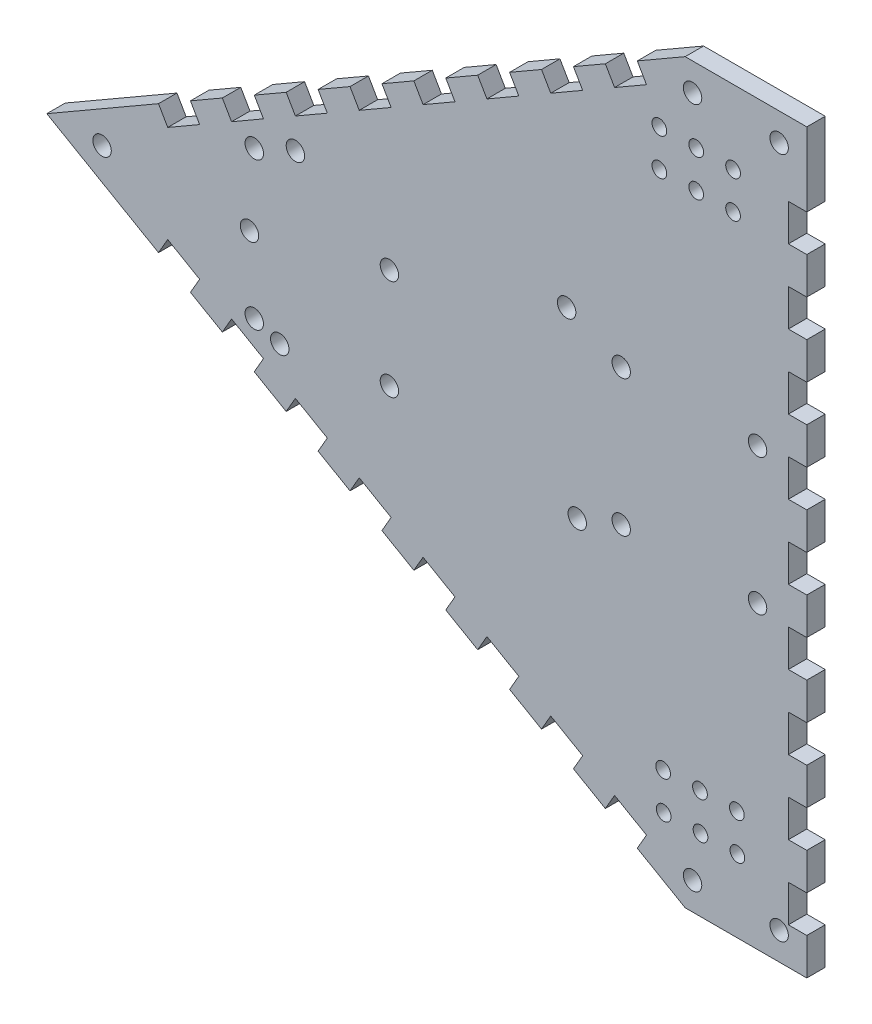
SolidWorks part; units mm, degrees
ref_plane "Front Plane" through (0, 0, 0) normal (0, 0, 1) x (1, 0, 0)
ref_plane "Top Plane" through (0, 0, 0) normal (0, 1, 0) x (1, 0, 0)
ref_plane "Right Plane" through (0, 0, 0) normal (1, 0, 0) x (0, 0, -1)
sketch "Sketch1" plane through (0, 0, 0) normal (0, 0, 1) x (1, 0, 0)
  line L0 (2.5, 0) -> (-30.5, 0)
  line L1 (2.5, 0) -> (-30.5, 0)
  line L2 (2.5, 0) -> (2.5, -200)
  line L3 (2.5, -200) -> (-30.5, -200)
  line L4 (-17.5, -20) -> (-27.5, -20) construction
  line L5 (-203.7051, -100) -> (-30.5, 0)
  line L7 (-30.5, -200) -> (-203.7051, -100)
  line L8 (-201.1315, -101.4859) -> (2.5, -100) construction
  line L9 (-2.5, 0) -> (2.5, 0)
  line L10 (2.5, 0) -> (-2.5, 0)
  line L15 (2.5, 0) -> (-2.5, 0)
  circle A0 centre (-17.5, -20) radius 2
  circle A1 centre (-27.5, -20) radius 2
  circle A2 centre (-37.5, -20) radius 2
  circle A3 centre (-27.5, -30) radius 2
  circle A4 centre (-37.5, -30) radius 2
  circle A5 centre (-17.5, -30) radius 2
  circle A6 centre (-36.3283, -180.5752) radius 2
  circle A7 centre (-26.3294, -180.4293) radius 2
  circle A8 centre (-26.4753, -170.4303) radius 2
  circle A9 centre (-16.4764, -170.2844) radius 2
  circle A10 centre (-16.3304, -180.2833) radius 2
  circle A11 centre (-36.4742, -170.5763) radius 2
  dimension "D8" = 4
  dimension "D2" = 60
  dimension "D3" = 200
  dimension "D4" = 188.4551
  dimension "D5" = 200
  dimension "D11" = 10
  dimension "D9" = 3
  dimension "D10" = 2
extrude "Boss-Extrude1" add sketch "Sketch1" along normal blind 5
sketch "Sketch2" plane through (0, 0, 5) normal (0, 0, 1) x (1, 0, 0)
  line L3 (-2.5, -100) -> (-136.8791, -100) construction
  circle A0 centre (-188.7051, -100) radius 2.5
  circle A1 centre (-5, -192.5) radius 2.5
  circle A2 centre (-10.85, -118.6057) radius 2.5
  circle A3 centre (-47.85, -118.6057) radius 2.5
  circle A4 centre (-5, -7.5) radius 2.5
  circle A5 centre (-47.85, -81.6057) radius 2.5
  circle A6 centre (-28.4904, -192.5) radius 2.5
  circle A7 centre (-10.85, -81.6057) radius 2.5
  circle A8 centre (-28.4904, -7.5) radius 2.5
  point P13 (2.5, -100.4557)
  dimension "D6" = 5
  dimension "D9" = 2
  dimension "D5" = 5
  dimension "D10" = 5
  dimension "D11" = 2
  dimension "D4" = 5
extrude "Cut-Extrude1" cut sketch "Sketch2" against normal through all both and the other way through all
sketch "Sketch3" plane through (0, 0, 5) normal (0, 0, 1) x (1, 0, 0)
  line L0 (-121.4327, -52.5) -> (-112.7724, -47.5)
  line L1 (-112.7724, -47.5) -> (-110.2724, -51.8301)
  line L2 (-110.2724, -51.8301) -> (-118.9327, -56.8301)
  line L3 (-118.9327, -56.8301) -> (-121.4327, -52.5)
  line L4 (-101.6122, -46.8301) -> (-104.1122, -42.5)
  line L5 (-92.9519, -41.8301) -> (-101.6122, -46.8301)
  line L6 (-95.4519, -37.5) -> (-92.9519, -41.8301)
  line L7 (-104.1122, -42.5) -> (-95.4519, -37.5)
  line L8 (-84.2917, -36.8301) -> (-86.7917, -32.5)
  line L9 (-75.6314, -31.8301) -> (-84.2917, -36.8301)
  line L10 (-78.1314, -27.5) -> (-75.6314, -31.8301)
  line L11 (-86.7917, -32.5) -> (-78.1314, -27.5)
  line L12 (-66.9711, -26.8301) -> (-69.4711, -22.5)
  line L13 (-58.3109, -21.8301) -> (-66.9711, -26.8301)
  line L14 (-60.8109, -17.5) -> (-58.3109, -21.8301)
  line L15 (-69.4711, -22.5) -> (-60.8109, -17.5)
  line L16 (-49.6506, -16.8301) -> (-52.1506, -12.5)
  line L17 (-40.9904, -11.8301) -> (-49.6506, -16.8301)
  line L18 (-43.4904, -7.5) -> (-40.9904, -11.8301)
  line L19 (-52.1506, -12.5) -> (-43.4904, -7.5)
  line L20 (-136.2532, -66.8301) -> (-138.7532, -62.5)
  line L21 (-127.5929, -61.8301) -> (-136.2532, -66.8301)
  line L22 (-130.0929, -57.5) -> (-127.5929, -61.8301)
  line L23 (-138.7532, -62.5) -> (-130.0929, -57.5)
  line L24 (-153.5737, -76.8301) -> (-156.0737, -72.5)
  line L25 (-144.9134, -71.8301) -> (-153.5737, -76.8301)
  line L26 (-147.4134, -67.5) -> (-144.9134, -71.8301)
  line L27 (-156.0737, -72.5) -> (-147.4134, -67.5)
  line L28 (-170.8942, -86.8301) -> (-173.3942, -82.5)
  line L29 (-162.2339, -81.8301) -> (-170.8942, -86.8301)
  line L30 (-164.7339, -77.5) -> (-162.2339, -81.8301)
  line L31 (-173.3942, -82.5) -> (-164.7339, -77.5)
  line L36 (-203.7051, -100) -> (-2.5, -100) construction
  line L39 (-112.7724, -152.5) -> (-110.2724, -148.1699)
  line L40 (-110.2724, -148.1699) -> (-118.9327, -143.1699)
  line L41 (-173.3942, -117.5) -> (-164.7339, -122.5)
  line L42 (-164.7339, -122.5) -> (-162.2339, -118.1699)
  line L43 (-156.0737, -127.5) -> (-147.4134, -132.5)
  line L44 (-147.4134, -132.5) -> (-144.9134, -128.1699)
  line L45 (-144.9134, -128.1699) -> (-153.5737, -123.1699)
  line L46 (-153.5737, -123.1699) -> (-156.0737, -127.5)
  line L47 (-138.7532, -137.5) -> (-130.0929, -142.5)
  line L48 (-130.0929, -142.5) -> (-127.5929, -138.1699)
  line L49 (-127.5929, -138.1699) -> (-136.2532, -133.1699)
  line L50 (-136.2532, -133.1699) -> (-138.7532, -137.5)
  line L55 (-162.2339, -118.1699) -> (-170.8942, -113.1699)
  line L56 (-170.8942, -113.1699) -> (-173.3942, -117.5)
  line L57 (-52.1506, -187.5) -> (-43.4904, -192.5)
  line L58 (-43.4904, -192.5) -> (-40.9904, -188.1699)
  line L59 (-40.9904, -188.1699) -> (-49.6506, -183.1699)
  line L60 (-49.6506, -183.1699) -> (-52.1506, -187.5)
  line L61 (-69.4711, -177.5) -> (-60.8109, -182.5)
  line L62 (-60.8109, -182.5) -> (-58.3109, -178.1699)
  line L63 (-58.3109, -178.1699) -> (-66.9711, -173.1699)
  line L64 (-66.9711, -173.1699) -> (-69.4711, -177.5)
  line L65 (-86.7917, -167.5) -> (-78.1314, -172.5)
  line L66 (-78.1314, -172.5) -> (-75.6314, -168.1699)
  line L67 (-75.6314, -168.1699) -> (-84.2917, -163.1699)
  line L68 (-84.2917, -163.1699) -> (-86.7917, -167.5)
  line L69 (-104.1122, -157.5) -> (-95.4519, -162.5)
  line L70 (-95.4519, -162.5) -> (-92.9519, -158.1699)
  line L71 (-92.9519, -158.1699) -> (-101.6122, -153.1699)
  line L72 (-101.6122, -153.1699) -> (-104.1122, -157.5)
  line L73 (-118.9327, -143.1699) -> (-121.4327, -147.5)
  line L74 (-121.4327, -147.5) -> (-112.7724, -152.5)
  line L75 (-2.5, -80) -> (-2.5, -90)
  line L76 (-2.5, -100) -> (2.5, -100)
  line L77 (-2.5, -100) -> (-2.5, -110)
  line L78 (-2.5, -110) -> (2.5, -110)
  line L79 (2.5, -100) -> (2.5, -110)
  line L80 (-2.5, -80) -> (2.5, -80)
  line L81 (2.5, -80) -> (2.5, -90)
  line L82 (-2.5, -90) -> (2.5, -90)
  line L83 (-2.5, -60) -> (-2.5, -70)
  line L84 (-2.5, -60) -> (2.5, -60)
  line L85 (2.5, -60) -> (2.5, -70)
  line L86 (-2.5, -70) -> (2.5, -70)
  line L87 (-2.5, -40) -> (-2.5, -50)
  line L88 (-2.5, -40) -> (2.5, -40)
  line L89 (2.5, -40) -> (2.5, -50)
  line L90 (-2.5, -50) -> (2.5, -50)
  line L91 (-2.5, -20) -> (-2.5, -30)
  line L92 (-2.5, -20) -> (2.5, -20)
  line L93 (2.5, -20) -> (2.5, -30)
  line L94 (-2.5, -30) -> (2.5, -30)
  line L99 (-2.5, -120) -> (-2.5, -130)
  line L100 (-2.5, -120) -> (2.5, -120)
  line L101 (2.5, -120) -> (2.5, -130)
  line L102 (-2.5, -130) -> (2.5, -130)
  line L103 (-2.5, -140) -> (-2.5, -150)
  line L104 (-2.5, -140) -> (2.5, -140)
  line L105 (2.5, -140) -> (2.5, -150)
  line L106 (-2.5, -150) -> (2.5, -150)
  line L107 (-2.5, -160) -> (-2.5, -170)
  line L108 (-2.5, -160) -> (2.5, -160)
  line L109 (2.5, -160) -> (2.5, -170)
  line L110 (-2.5, -170) -> (2.5, -170)
  line L111 (-2.5, -180) -> (-2.5, -190)
  line L112 (-2.5, -180) -> (2.5, -180)
  line L113 (2.5, -180) -> (2.5, -190)
  line L114 (-2.5, -190) -> (2.5, -190)
  line L129 (-179.5544, -91.8301) -> (-188.2147, -96.8301) [skipped]
  line L130 (-182.0544, -87.5) -> (-179.5544, -91.8301) [skipped]
  line L131 (-188.2147, -96.8301) -> (-190.7147, -92.5) [skipped]
  line L132 (-190.7147, -92.5) -> (-182.0544, -87.5) [skipped]
  line L133 (-2.5, 0) -> (2.5, 0) [skipped]
  line L134 (2.5, 0) -> (2.5, -10) [skipped]
  line L135 (-2.5, 0) -> (-2.5, -10) [skipped]
  line L136 (-2.5, -10) -> (2.5, -10) [skipped]
  circle A0 centre (-136.2532, -75) radius 2.5
  circle A1 centre (-62.6532, -75) radius 2.5
  circle A2 centre (-140.4956, -122.5) radius 2.5
  circle A3 centre (-59.7756, -123.1699) radius 2.5
  circle A4 centre (-110.7456, -117.5) radius 2.5
  circle A5 centre (-110.7456, -90.25) radius 2.5
  circle A6 centre (-148.7051, -100) radius 2.5
  circle A7 centre (-147.4134, -80) radius 2.5
  circle A8 centre (-147.4134, -120) radius 2.5
  point P15 (-151.7436, -130)
  point P16 (-134.423, -140)
  point P23 (-169.0641, -120)
  point P24 (-186.3846, -110)
  point P29 (-47.8205, -190)
  point P46 (-117.1025, -50)
  point P52 (-99.782, -40)
  point P57 (-82.4615, -30)
  point P62 (-65.141, -20)
  point P67 (-47.8205, -10)
  point P72 (-134.423, -60)
  point P77 (-151.7436, -70)
  point P82 (-169.0641, -80)
  point P87 (-186.3846, -90)
  point P91 (-65.141, -180)
  point P92 (-82.4615, -170)
  point P93 (-99.782, -160)
  point P94 (-117.1025, -150)
  point P116 (-147.4134, -100)
  dimension "D8" = 5
  dimension "D9" = 5
  dimension "D10" = 73.6
  dimension "D11" = 5
  dimension "D12" = 47.5
  dimension "D13" = 25
  dimension "D14" = 5
  dimension "D15" = 80.72
  dimension "D16" = 5
  dimension "D17" = 5
  dimension "D18" = 27.25
  dimension "D19" = 29.75
  dimension "D20" = 29.75
  dimension "D21" = 5
  dimension "D2" = 5
  dimension "D3" = 10
  dimension "D4" = 5
  dimension "D5" = 10
  dimension "D6" = 5
  dimension "D1" = 6
  dimension "D7" = 5
extrude "Cut-Extrude5" cut sketch "Sketch3" against normal through all both and the other way through all
